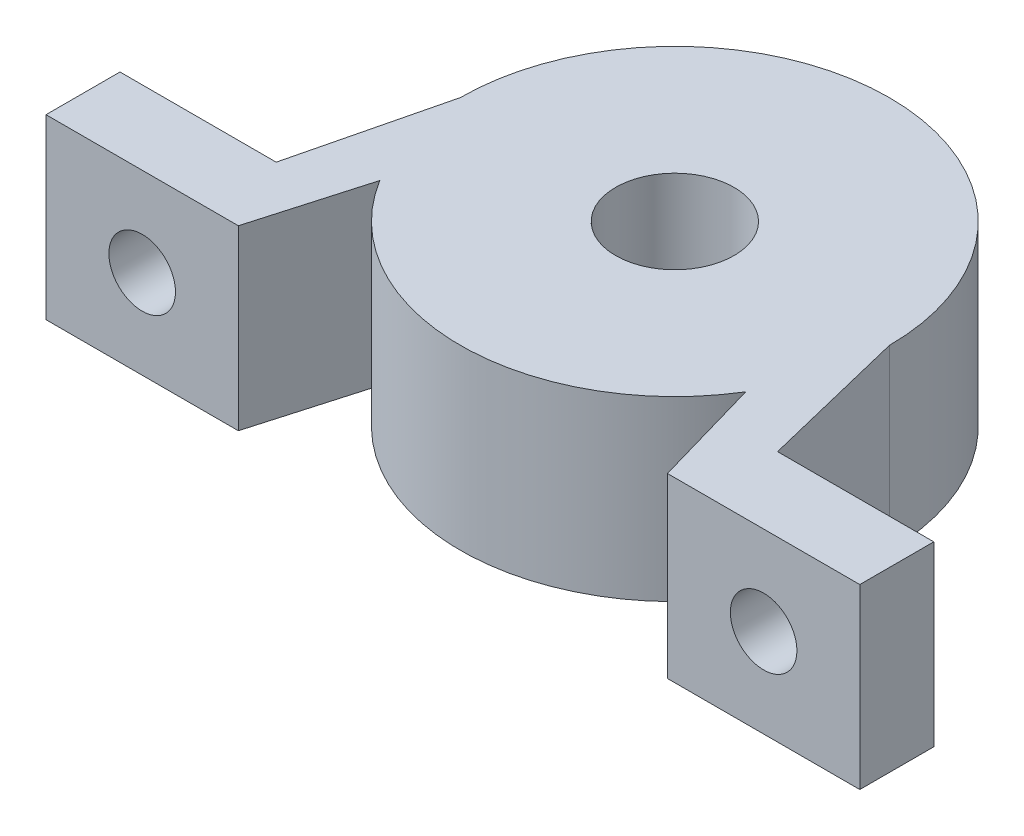
SolidWorks part; units mm, degrees
ref_plane "Front Plane" through (0, 0, 0) normal (0, 0, 1) x (1, 0, 0)
ref_plane "Top Plane" through (0, 0, 0) normal (0, 1, 0) x (1, 0, 0)
ref_plane "Right Plane" through (0, 0, 0) normal (1, 0, 0) x (0, 0, -1)
sketch "Sketch1" plane through (0, 0, 0) normal (0, 1, 0) x (1, 0, 0)
  line L0 (0, 0) -> (0, -36.3749) construction
  line L1 (-27.5, -10) -> (-27.5, -15)
  line L2 (-27.5, -15) -> (-14.5, -15)
  line L3 (-27.5, -10) -> (-16.9429, -10)
  line L4 (-16.9429, -10) -> (-14.5, 0)
  line L5 (-14.5, -15) -> (-12.3664, -7.5711)
  line L6 (16.9429, -10) -> (14.5, 0)
  line L7 (14.5, -15) -> (12.3664, -7.5711)
  line L8 (27.5, -10) -> (16.9429, -10)
  line L9 (27.5, -15) -> (14.5, -15)
  line L10 (27.5, -10) -> (27.5, -15)
  arc A0 (-12.3664, -7.5711) -> (12.3664, -7.5711) centre (0, 0) ccw
  circle A1 centre (0, 0) radius 4
  arc A2 (14.5, 0) -> (-14.5, 0) centre (0, 0) ccw
  dimension "D1" = 29
  dimension "D2" = 8
  dimension "D3" = 5
  dimension "D4" = 27.5
  dimension "D5" = 15
  dimension "D6" = 13
extrude "Boss-Extrude1" add sketch "Sketch1" along normal blind 12
sketch "Sketch2" plane through (0, 0, 15) normal (0, 0, 1) x (1, 0, 0)
  line L0 (-21, 12) -> (-21, 0) construction
  line L1 (-27.5, 12) -> (-14.5, 12) construction
  line L2 (-27.5, 0) -> (-14.5, 0) construction
  line L3 (21, 12) -> (21, 0) construction
  line L4 (14.5, 12) -> (27.5, 12) construction
  line L5 (14.5, 0) -> (27.5, 0) construction
  circle A0 centre (-21, 6) radius 2.25
  circle A1 centre (21, 6) radius 2.25
  dimension "D1" = 4.5
  dimension "D2" = 4.5
  dimension "D3" = 42
extrude "Cut-Extrude1" cut sketch "Sketch2" against normal blind 12
